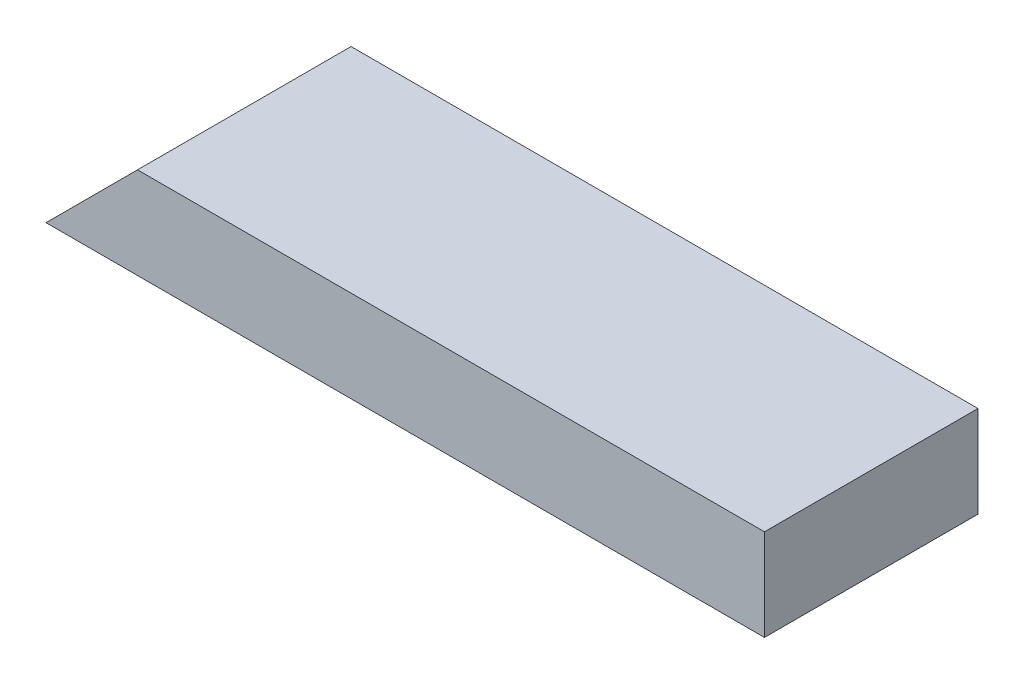
SolidWorks part; units mm, degrees
material "Pine"
ref_plane "Front Plane" through (0, 0, 0) normal (0, 0, 1) x (1, 0, 0)
ref_plane "Top Plane" through (0, 0, 0) normal (0, 1, 0) x (1, 0, 0)
ref_plane "Right Plane" through (0, 0, 0) normal (1, 0, 0) x (0, 0, -1)
sketch "Sketch1" plane through (0, 0, 0) normal (0, 1, 0) x (1, 0, 0)
  line L1 (0, 0) -> (299.0977, 0)
  line L2 (0, 0) -> (0, 88.9)
  line L3 (0, 88.9) -> (299.0977, 88.9)
  line L4 (299.0977, 0) -> (299.0977, 88.9)
  dimension "D1" = 88.9
  dimension "D2" = 299.0977
extrude "Boss-Extrude1" add sketch "Sketch1" along normal blind 38.1
sketch "Sketch2" plane through (0, 0, 0) normal (0, 0, 1) x (1, 0, 0)
  line L0 (0, 0) -> (38.1, 38.1)
  line L1 (0, 38.1) -> (299.0977, 38.1) construction
  line L2 (38.1, 38.1) -> (0, 38.1)
  line L3 (0, 38.1) -> (0, 0)
  dimension "D1" = 38.1
  dimension "D2" = 38.1
extrude "Cut-Extrude1" cut sketch "Sketch2" against normal through all
